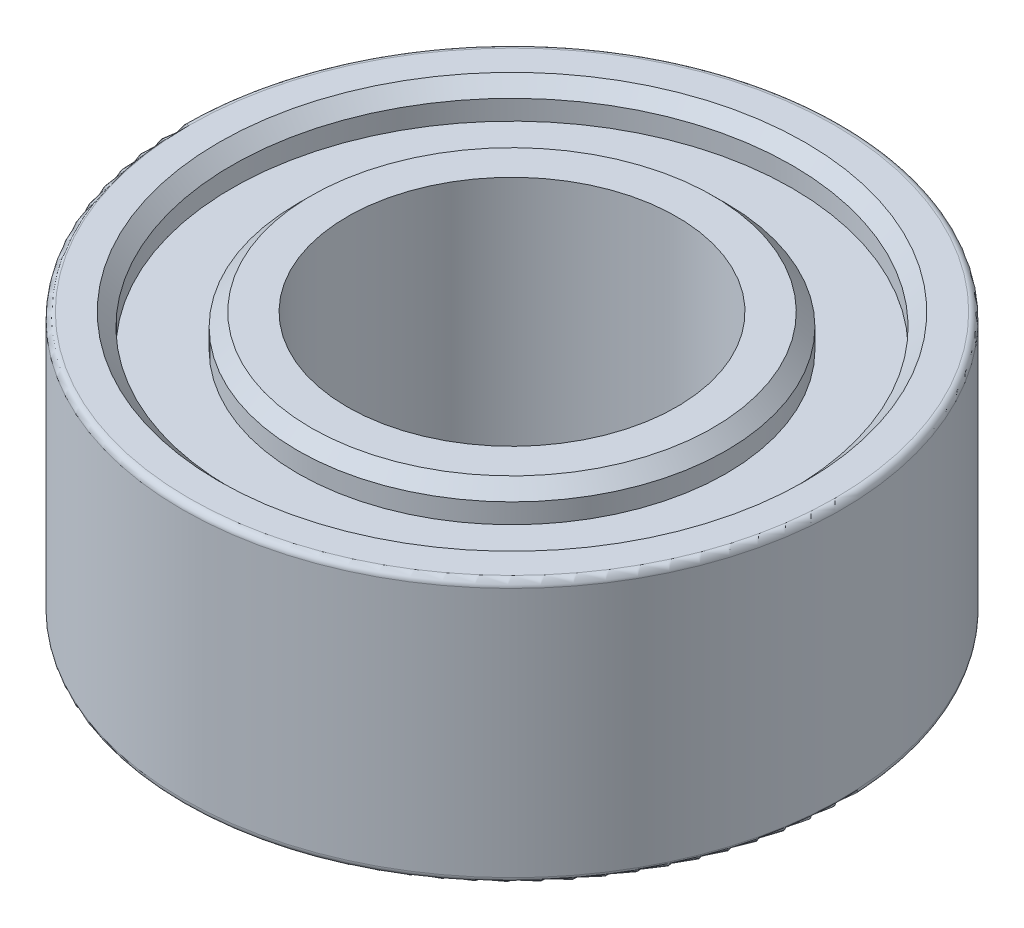
SolidWorks part; units mm, degrees
material "Plain Carbon Steel"
ref_plane "Front Plane" through (0, 0, 0) normal (0, 0, 1) x (1, 0, 0)
ref_plane "Top Plane" through (0, 0, 0) normal (0, 1, 0) x (1, 0, 0)
ref_plane "Right Plane" through (0, 0, 0) normal (1, 0, 0) x (0, 0, -1)
sketch "Sketch2" plane through (0, 0, 0) normal (0, 1, 0) x (1, 0, 0)
  circle A0 centre (0, 0) radius 5
  circle A1 centre (0, 0) radius 2.5
  dimension "D1" = 10
  dimension "D2" = 5
extrude "Boss-Extrude1" add sketch "Sketch2" along normal mid plane 4
sketch "Sketch3" plane through (0, 2, 0) normal (0, 1, 0) x (1, 0, 0)
  circle A0 centre (0, 0) radius 3.25
  circle A1 centre (0, 0) radius 4.25
  circle A2 centre (0, 0) radius 2.5 construction
  dimension "D1" = 0.75
  dimension "D2" = 1
extrude "Cut-Extrude1" cut sketch "Sketch3" against normal blind 0.5
mirror "Mirror1" about plane through (0, 0, 0) normal (0, 1, 0) of "Cut-Extrude1"
chamfer "Chamfer1" distance 0.2 angle 45 4 edges at (0, 2, 3.25) (0, 2, 4.25) (0, -2, 4.25) (0, -2, 3.25)
fillet "Fillet1" radius 0.1 2 edges at (0, -2, 5) (0, 2, 5)
